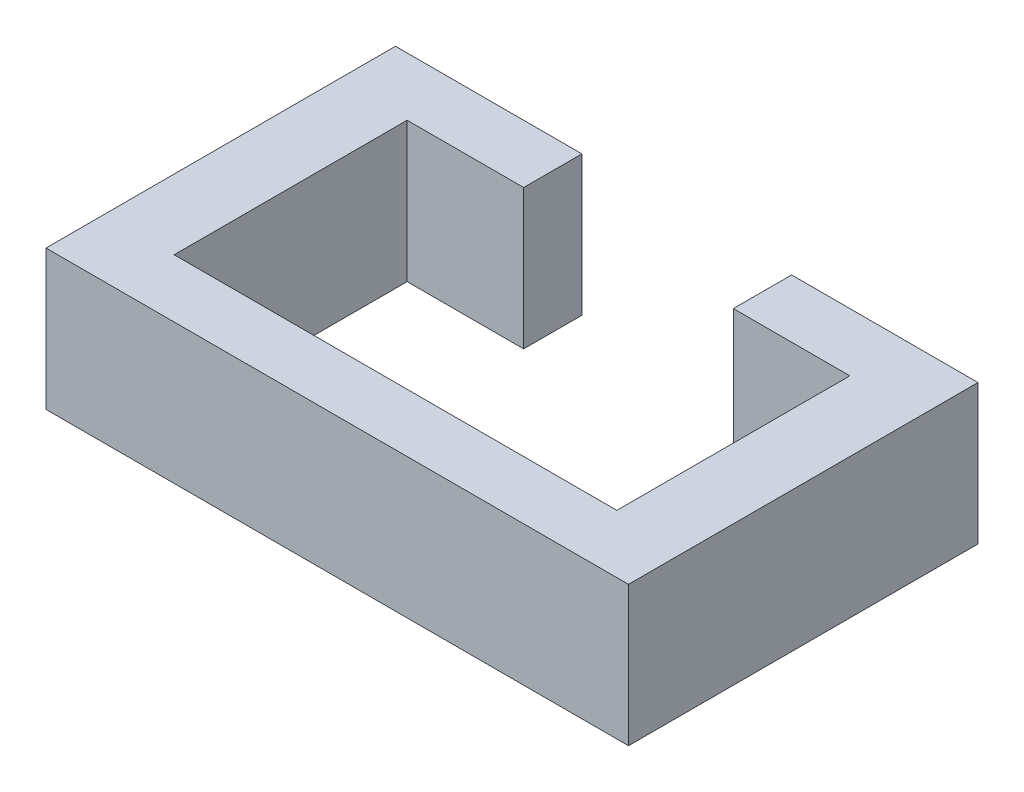
SolidWorks part; units mm, degrees
ref_plane "Front Plane" through (0, 0, 0) normal (0, 0, 1) x (1, 0, 0)
ref_plane "Top Plane" through (0, 0, 0) normal (0, 1, 0) x (1, 0, 0)
ref_plane "Right Plane" through (0, 0, 0) normal (1, 0, 0) x (0, 0, -1)
sketch "Sketch1" plane through (0, 0, 0) normal (0, 1, 0) x (1, 0, 0)
  line L1 (-25, 10) -> (-9, 10)
  line L2 (-9, 10) -> (-9, 5)
  line L3 (-9, 5) -> (-19, 5)
  line L4 (-19, 5) -> (-19, -15)
  line L5 (-19, -15) -> (19, -15)
  line L6 (19, -15) -> (19, 5)
  line L7 (19, 5) -> (9, 5)
  line L8 (9, 5) -> (9, 10)
  line L9 (9, 10) -> (25, 10)
  line L10 (25, 10) -> (25, -20)
  line L11 (25, -20) -> (-25, -20)
  line L13 (-25, 10) -> (-25, -20)
  line L14 (0, -20) -> (0, 0) construction
  line L15 (-19, -15) -> (-19, -20)
  point P14 (0, -15)
  dimension "D1" = 20
  dimension "D2" = 5
  dimension "D3" = 50
  dimension "D4" = 10
  dimension "D5" = 38
  dimension "D6" = 5
  dimension "D7" = 20
extrude "Boss-Extrude1" add sketch "Sketch1" along normal blind 12 contours L15 L4 L3 L2 L1 L13 L11 | L11 L14 L5 L15 | L14 L11 L10 L9 L8 L7 L6 L5
